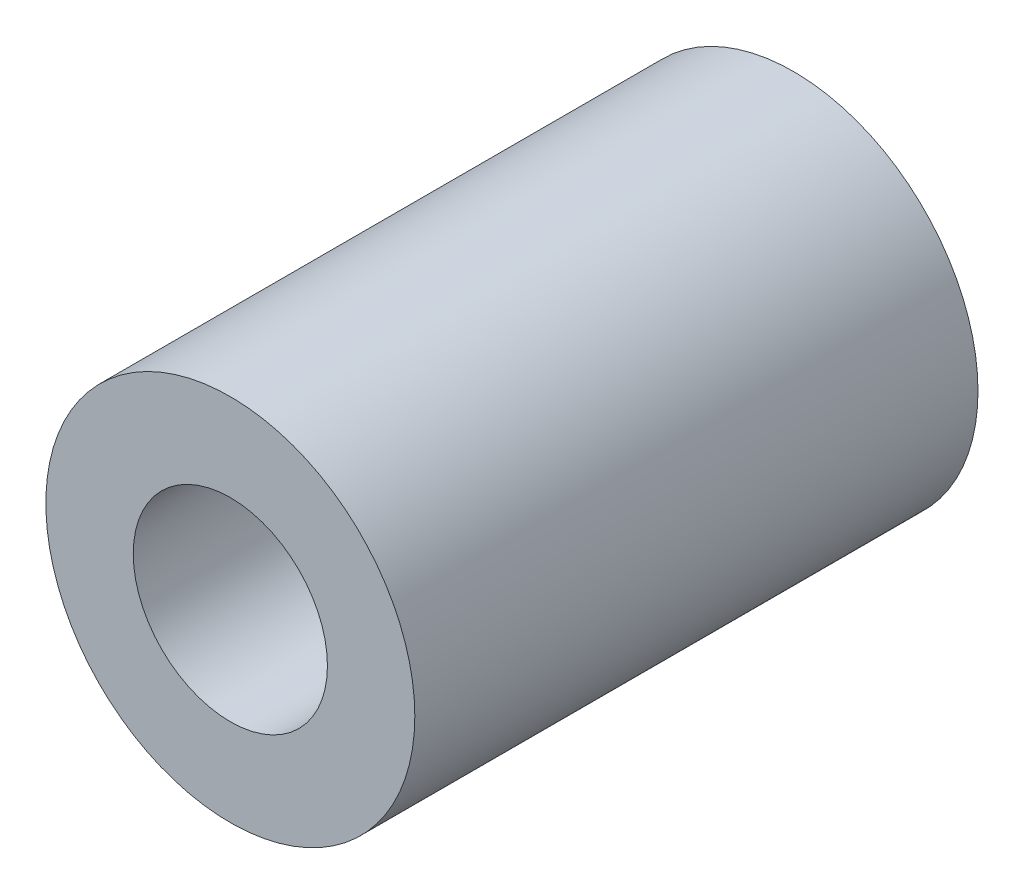
SolidWorks part; units mm, degrees
ref_plane "Front Plane" through (0, 0, 0) normal (0, 0, 1) x (1, 0, 0)
ref_plane "Top Plane" through (0, 0, 0) normal (0, 1, 0) x (1, 0, 0)
ref_plane "Right Plane" through (0, 0, 0) normal (1, 0, 0) x (0, 0, -1)
sketch "Sketch1" plane through (0, 0, 0) normal (0, 0, 1) x (1, 0, 0)
  circle A0 centre (0, 0) radius 5
  circle A1 centre (0, 0) radius 9.5
  dimension "D1" = 10
  dimension "D2" = 19
extrude "Boss-Extrude1" add sketch "Sketch1" along normal blind 29
